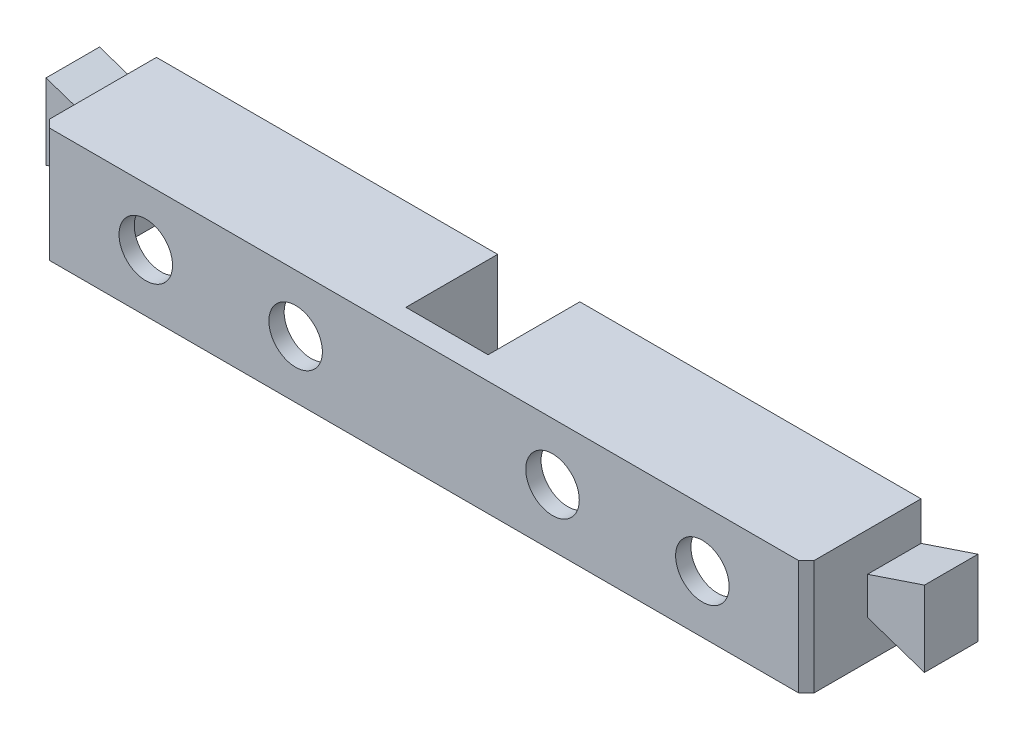
SolidWorks part; units mm, degrees
ref_plane "Front Plane" through (0, 0, 0) normal (0, 0, 1) x (1, 0, 0)
ref_plane "Top Plane" through (0, 0, 0) normal (0, 1, 0) x (1, 0, 0)
ref_plane "Right Plane" through (0, 0, 0) normal (1, 0, 0) x (0, 0, -1)
sketch "Sketch1" plane through (0, 0, 0) normal (0, 0, 1) x (1, 0, 0)
  line L1 (-50, -7.5) -> (50, -7.5)
  line L2 (-50, -7.5) -> (-50, 7.5)
  line L3 (-50, 7.5) -> (50, 7.5)
  line L4 (50, -7.5) -> (50, 7.5)
  line L5 (-50, -7.5) -> (50, 7.5) construction
  line L6 (-50, 7.5) -> (50, -7.5) construction
  point P0 (0, 0)
  dimension "D1" = 100
  dimension "D2" = 15
extrude "Body" add sketch "Sketch1" along normal blind 15
sketch "Sketch2" plane through (0, 0, 0) normal (0, 0, 1) x (1, 0, 0)
  line L0 (-50, 0) -> (50, 0) construction
  line L1 (-50, 7.5) -> (-50, -7.5) construction
  line L2 (50, -7.5) -> (50, 7.5) construction
  line L3 (-50, 0) -> (-50, 2.45)
  line L4 (-50, 2.45) -> (-57.45, 4.95)
  line L6 (-57.45, -4.95) -> (-50, -2.45)
  line L7 (-50, -2.45) -> (-50, 0)
  line L8 (-50, 0) -> (-63.3586, 0) construction
  line L9 (-57.45, 4.95) -> (-57.45, 0)
  line L10 (-57.45, 0) -> (-57.45, -4.95)
  line L11 (0, 7.5) -> (0, -7.5) construction
  line L12 (50, 7.5) -> (-50, 7.5) construction
  line L13 (-50, -7.5) -> (50, -7.5) construction
  line L14 (50, 0) -> (63.3586, 0) construction
  line L15 (57.45, 0) -> (57.45, -4.95)
  line L16 (57.45, 4.95) -> (57.45, 0)
  line L17 (50, -2.45) -> (50, 0)
  line L18 (57.45, -4.95) -> (50, -2.45)
  line L19 (50, 2.45) -> (57.45, 4.95)
  line L20 (50, 0) -> (50, 2.45)
  dimension "D1" = 2.45
  dimension "D2" = 2.45
  dimension "D3" = 4.95
  dimension "D4" = 4.95
  dimension "D5" = 7.45
extrude "Click" add sketch "Sketch2" along normal blind 7
chamfer "Click Chamfer" distance 1 angle 45 2 edges at (-50, 0, 15) (50, 0, 15)
sketch "Sketch3" plane through (0, -7.5, 0) normal (0, -1, 0) x (1, 0, 0)
  line L0 (-46, 0) -> (-46, 13)
  line L1 (-50, 0) -> (50, 0) construction
  line L2 (-46, 13) -> (46, 13)
  line L3 (46, 13) -> (46, 0)
  line L4 (46, 0) -> (-46, 0)
  line L5 (-49, 15) -> (49, 15) construction
  line L6 (50, 14) -> (50, 0) construction
  line L7 (-50, 14) -> (-50, 0) construction
  dimension "D1" = 2
  dimension "D2" = 4
  dimension "D3" = 4
extrude "Cut-Extrude1" cut sketch "Sketch3" against normal blind 13
sketch "Sketch4" plane through (0, 0, 15) normal (0, 0, 1) x (1, 0, 0)
  line L0 (-49, 0) -> (49, 0) construction
  line L1 (-49, 7.5) -> (-49, -7.5) construction
  line L2 (49, -7.5) -> (49, 7.5) construction
  line L3 (0, 7.5) -> (0, -7.5) construction
  line L4 (49, 7.5) -> (-49, 7.5) construction
  line L5 (-49, -7.5) -> (49, -7.5) construction
  circle A0 centre (-16.8, 0) radius 3.5
  circle A1 centre (-36.4, 0) radius 3.5
  circle A2 centre (16.8, 0) radius 3.5
  circle A3 centre (36.4, 0) radius 3.5
  dimension "D1" = 7
  dimension "D2" = 7
  dimension "D3" = 7
  dimension "D4" = 7
  dimension "D5" = 16.8
  dimension "D6" = 16.8
  dimension "D7" = 19.6
  dimension "D8" = 19.6
extrude "Cut-Extrude2" cut sketch "Sketch4" against normal blind 13
sketch "Sketch5" plane through (0, 7.5, 0) normal (0, 1, 0) x (1, 0, 0)
  line L0 (0, 0) -> (0, -15) construction
  line L1 (50, 0) -> (-50, 0) construction
  line L2 (49, -15) -> (-49, -15) construction
  line L4 (-5.375, -12) -> (5.375, -12)
  line L5 (-5.375, -12) -> (-5.375, 0)
  line L6 (-5.375, 0) -> (5.375, 0)
  line L7 (5.375, -12) -> (5.375, 0)
  line L8 (-5.375, -12) -> (5.375, 0) construction
  line L9 (-5.375, 0) -> (5.375, -12) construction
  point P6 (0, -6)
  dimension "D1" = 10.75
  dimension "D2" = 12
extrude "Cut-Extrude3" cut sketch "Sketch5" against normal blind 10
sketch "Sketch6" plane through (0, 0, 13) normal (0, 0, -1) x (-1, 0, 0)
  line L0 (-46, -7.5) -> (46, -7.5) construction
  line L1 (-5.375, 5.5) -> (5.375, 5.5)
  line L2 (-5.375, 5.5) -> (-5.375, -7.5)
  line L3 (-5.375, -7.5) -> (5.375, -7.5)
  line L4 (5.375, 5.5) -> (5.375, -7.5)
extrude "Boss-Extrude1" add sketch "Sketch6" along normal up to surface (1 mm away) up to face at (0, 6.5, 12)
sketch "Sketch7" plane through (0, 0, 13) normal (0, 0, -1) x (-1, 0, 0)
  line L0 (5.375, -7.5) -> (46, -7.5) construction
  line L1 (5.375, 5.5) -> (7.375, 5.5)
  line L2 (5.375, 5.5) -> (5.375, -7.5)
  line L3 (5.375, -7.5) -> (7.375, -7.5)
  line L4 (7.375, 5.5) -> (7.375, -7.5)
  dimension "D1" = 2
extrude "Boss-Extrude2" add sketch "Sketch7" along normal up to surface (13 mm away) up to face at (-41.765, 1.1, 0)
sketch "Sketch8" plane through (0, 0, 13) normal (0, 0, -1) x (-1, 0, 0)
  line L1 (-5.375, 5.5) -> (-7.375, 5.5)
  line L2 (-5.375, 5.5) -> (-5.375, 0.5)
  line L3 (-5.375, 0.5) -> (-7.375, 0.5)
  line L4 (-7.375, 5.5) -> (-7.375, 0.5)
  dimension "D1" = 2
  dimension "D2" = 5
extrude "Boss-Extrude3" add sketch "Sketch8" along normal up to surface (13 mm away) up to face at (41.765, 1.1, 0)
